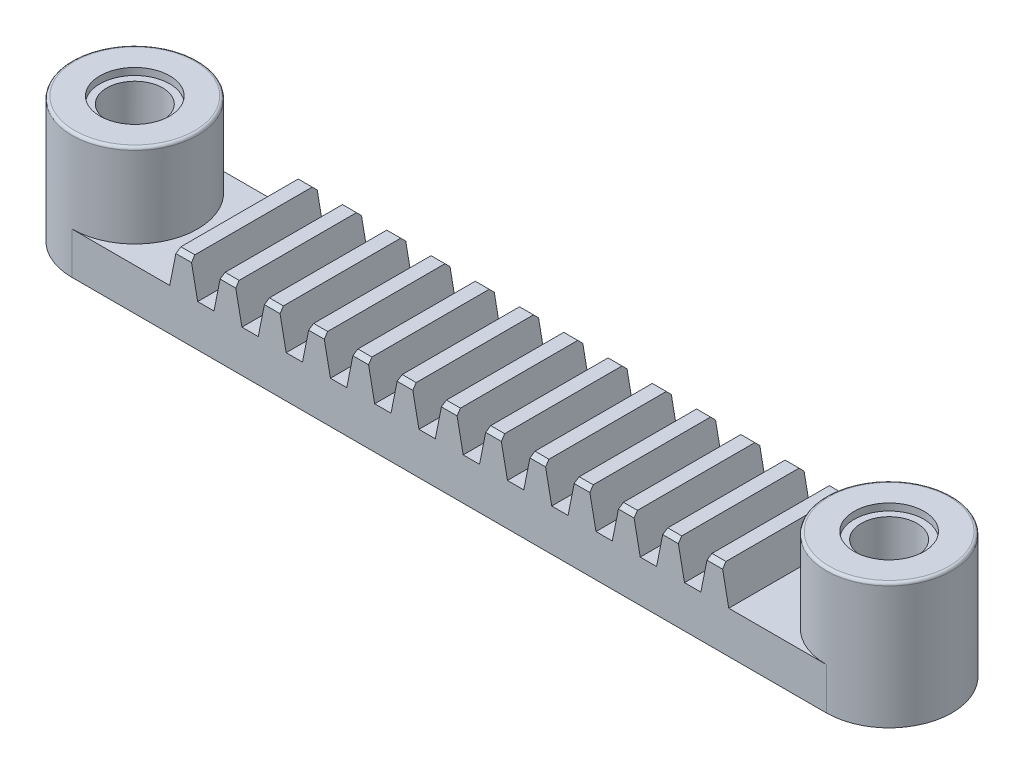
SolidWorks part; units mm, degrees
material "PBT General Purpose"
ref_plane "Front Plane" through (0, 0, 0) normal (0, 0, 1) x (1, 0, 0)
ref_plane "Top Plane" through (0, 0, 0) normal (0, 1, 0) x (1, 0, 0)
ref_plane "Right Plane" through (0, 0, 0) normal (1, 0, 0) x (0, 0, -1)
sketch "Sketch1" plane through (0, 0, 0) normal (0, 1, 0) x (1, 0, 0)
  line L0 (-27, 0) -> (27, 0) construction
  line L1 (-27, 4.5) -> (27, 4.5)
  line L2 (-27, -4.5) -> (27, -4.5)
  arc A0 (-27, 4.5) -> (-27, -4.5) centre (-27, 0) ccw
  arc A1 (27, -4.5) -> (27, 4.5) centre (27, 0) ccw
  point P2 (0, 0)
  dimension "D1" = 4.5
  dimension "D2" = 54
extrude "Boss-Extrude1" add sketch "Sketch1" against normal blind 3
sketch "Sketch2" plane through (0, 0, 0) normal (0, 1, 0) x (1, 0, 0)
  circle A0 centre (-27, 0) radius 4.5
  circle A1 centre (27, 0) radius 4.5
  arc A4 (27, -4.5) -> (27, 4.5) centre (27, 0) ccw construction
extrude "Boss-Extrude2" add sketch "Sketch2" along normal blind 6
sketch "Sketch3" plane through (0, 6, 0) normal (0, 1, 0) x (1, 0, 0)
  line L0 (0, -4.95) -> (0, 4.95) construction
  circle A0 centre (-27, 0) radius 2
  circle A2 centre (27, 0) radius 2
  dimension "D1" = 4
extrude "Cut-Extrude1" cut sketch "Sketch3" against normal up to next
sketch "Sketch4" plane through (0, 6, 0) normal (0, 1, 0) x (1, 0, 0)
  line L0 (0, -4.95) -> (0, 4.95) construction
  circle A0 centre (-27, 0) radius 2.5
  circle A1 centre (27, 0) radius 2.5
  dimension "D1" = 5
extrude "Cut-Extrude2" cut sketch "Sketch4" against normal blind 0.5
ref_plane "Plane1" through (0, 1.5, 0) normal (0, -1, 0) x (-1, 0, 0)
mirror "Mirror1" about plane through (0, 1.5, 0) normal (0, -1, 0) of "Cut-Extrude2"
sketch "Sketch20" plane through (0, 0, 0) normal (0, 1, 0) x (1, 0, 0)
  line L0 (-19, 0) -> (19, 0) construction
  line L1 (-19, 4.5) -> (-19, -4.5) construction
  line L2 (27, 4.5) -> (-27, 4.5) construction
  line L3 (-27, -4.5) -> (27, -4.5) construction
  line L4 (19, 4.5) -> (19, -4.5) construction
  point P9 (0, 0)
  dimension "D1" = 38
sketch "Sketch21" plane through (0, 0, 4.5) normal (0, 0, 1) x (1, 0, 0)
  line L0 (-20, 0) -> (-18, 0)
  line L1 (-27, 0) -> (27, 0) construction
  line L2 (-19, 0) -> (19, 0) construction
  line L3 (-20, 0) -> (-19.5, 2.5)
  line L4 (-19.5, 2.5) -> (-18.5, 2.5)
  line L5 (-18.5, 2.5) -> (-18, 0)
  line L6 (-16.8316, 0) -> (-16.3316, 2.5)
  line L7 (-16.3316, 2.5) -> (-15.3316, 2.5)
  line L8 (-15.3316, 2.5) -> (-14.8316, 0)
  line L9 (-16.8316, 0) -> (-14.8316, 0)
  line L10 (-13.6632, 0) -> (-13.1632, 2.5)
  line L11 (-13.1632, 2.5) -> (-12.1632, 2.5)
  line L12 (-12.1632, 2.5) -> (-11.6632, 0)
  line L13 (-13.6632, 0) -> (-11.6632, 0)
  line L14 (-10.4949, 0) -> (-9.9949, 2.5)
  line L15 (-9.9949, 2.5) -> (-8.9949, 2.5)
  line L16 (-8.9949, 2.5) -> (-8.4949, 0)
  line L17 (-10.4949, 0) -> (-8.4949, 0)
  line L18 (-7.3265, 0) -> (-6.8265, 2.5)
  line L19 (-6.8265, 2.5) -> (-5.8265, 2.5)
  line L20 (-5.8265, 2.5) -> (-5.3265, 0)
  line L21 (-7.3265, 0) -> (-5.3265, 0)
  line L22 (-4.1581, 0) -> (-3.6581, 2.5)
  line L23 (-3.6581, 2.5) -> (-2.6581, 2.5)
  line L24 (-2.6581, 2.5) -> (-2.1581, 0)
  line L25 (-4.1581, 0) -> (-2.1581, 0)
  line L26 (-0.9897, 0) -> (-0.4897, 2.5)
  line L27 (-0.4897, 2.5) -> (0.5103, 2.5)
  line L28 (0.5103, 2.5) -> (1.0103, 0)
  line L29 (-0.9897, 0) -> (1.0103, 0)
  line L30 (2.1787, 0) -> (2.6787, 2.5)
  line L31 (2.6787, 2.5) -> (3.6787, 2.5)
  line L32 (3.6787, 2.5) -> (4.1787, 0)
  line L33 (2.1787, 0) -> (4.1787, 0)
  line L34 (5.347, 0) -> (5.847, 2.5)
  line L35 (5.847, 2.5) -> (6.847, 2.5)
  line L36 (6.847, 2.5) -> (7.347, 0)
  line L37 (5.347, 0) -> (7.347, 0)
  line L38 (8.5154, 0) -> (9.0154, 2.5)
  line L39 (9.0154, 2.5) -> (10.0154, 2.5)
  line L40 (10.0154, 2.5) -> (10.5154, 0)
  line L41 (8.5154, 0) -> (10.5154, 0)
  line L42 (11.6838, 0) -> (12.1838, 2.5)
  line L43 (12.1838, 2.5) -> (13.1838, 2.5)
  line L44 (13.1838, 2.5) -> (13.6838, 0)
  line L45 (11.6838, 0) -> (13.6838, 0)
  line L46 (14.8522, 0) -> (15.3522, 2.5)
  line L47 (15.3522, 2.5) -> (16.3522, 2.5)
  line L48 (16.3522, 2.5) -> (16.8522, 0)
  line L49 (14.8522, 0) -> (16.8522, 0)
  line L50 (18.0206, 0) -> (18.5206, 2.5)
  line L51 (18.5206, 2.5) -> (19.5206, 2.5)
  line L52 (19.5206, 2.5) -> (20.0206, 0)
  line L53 (18.0206, 0) -> (20.0206, 0)
  line L54 (-20, 0) -> (-16.8316, 0) construction
  point P6 (-19, 0)
  point P7 (-19, 2.5)
  dimension "D1" = 2
  dimension "D2" = 1
  dimension "D3" = 2.5
  dimension "D5" = 3.1684
  dimension "D4" = 13
extrude "Boss-Extrude4" add sketch "Sketch21" against normal up to surface (9 mm away) up to face at (0, -1.5, -4.5)
chamfer "Chamfer1" distance 0.3 angle 45 26 edges at (-19, 2.5, -4.5) (-19, 2.5, 4.5) (-15.8316, 2.5, -4.5) (-15.8316, 2.5, 4.5) (-12.6632, 2.5, -4.5) (-12.6632, 2.5, 4.5) (-9.4949, 2.5, -4.5) (-9.4949, 2.5, 4.5) (-6.3265, 2.5, -4.5) (-6.3265, 2.5, 4.5) (-3.1581, 2.5, -4.5) (-3.1581, 2.5, 4.5) (0.0103, 2.5, -4.5) (0.0103, 2.5, 4.5) (3.1787, 2.5, -4.5) (3.1787, 2.5, 4.5) (6.347, 2.5, -4.5) (6.347, 2.5, 4.5) (9.5154, 2.5, -4.5) (9.5154, 2.5, 4.5) (19.0206, 2.5, -4.5) (19.0206, 2.5, 4.5) (12.6838, 2.5, -4.5) (12.6838, 2.5, 4.5) (15.8522, 2.5, -4.5) (15.8522, 2.5, 4.5)
fillet "Fillet1" radius 0.2 2 edges at (27, 6, 4.5) (-27, 6, 4.5)
